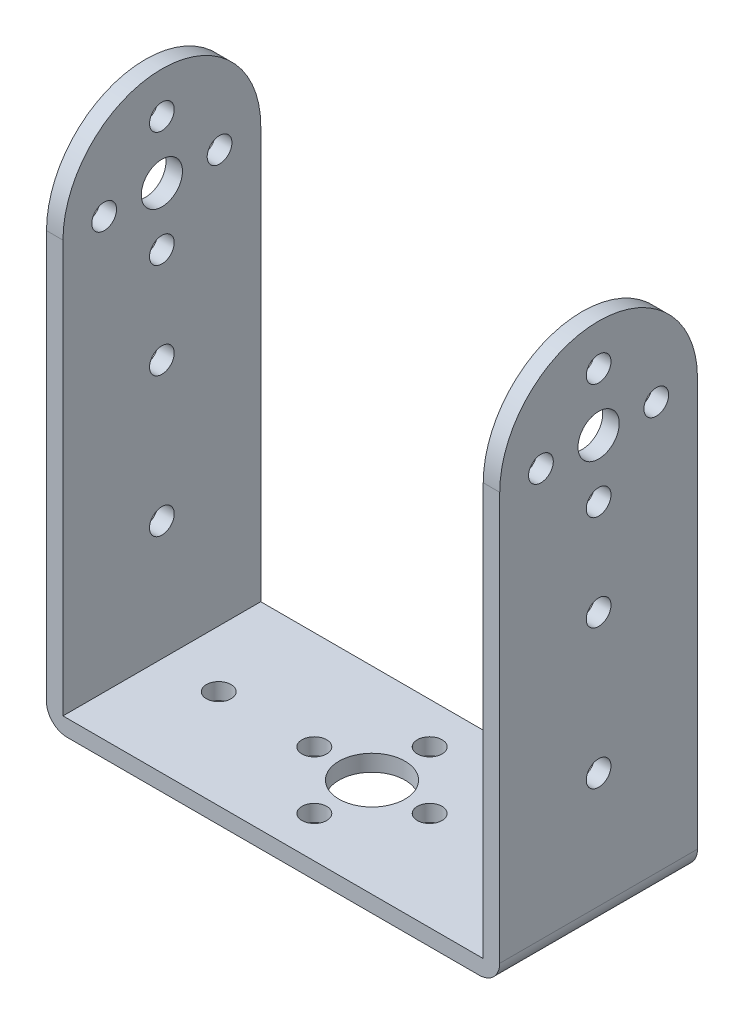
SolidWorks part; units mm, degrees
ref_plane "Front Plane" through (0, 0, 0) normal (0, 0, 1) x (1, 0, 0)
ref_plane "Top Plane" through (0, 0, 0) normal (0, 1, 0) x (1, 0, 0)
ref_plane "Right Plane" through (0, 0, 0) normal (1, 0, 0) x (0, 0, -1)
sketch "Sketch2" plane through (0, 0, 0) normal (0, 1, 0) x (1, 0, 0)
  line L0 (0, 1.0872) -> (0, 23.0088) construction
  line L1 (-27.5, -12) -> (27.5, -12)
  line L2 (-27.5, -12) -> (-27.5, 12)
  line L3 (-27.5, 12) -> (27.5, 12)
  line L4 (27.5, -12) -> (27.5, 12)
  line L5 (-27.5, -12) -> (27.5, 12) construction
  line L6 (-27.5, 12) -> (27.5, -12) construction
  line L7 (0, 0) -> (61.8612, 0) construction
  circle A0 centre (0, 0) radius 4
  circle A1 centre (0, 0) radius 7 construction
  circle A2 centre (0, 7) radius 1.5
  circle A3 centre (7, 0) radius 1.5
  circle A4 centre (0, -7) radius 1.5
  circle A5 centre (-7, 0) radius 1.5
  circle A6 centre (-18.6, 0) radius 1.5
  circle A7 centre (18.6, 0) radius 1.5
  point P0 (0, 0)
  point P24 (0, 0)
  dimension "D3" = 8
  dimension "D4" = 14
  dimension "D5" = 3
  dimension "D7" = 3
  dimension "D8" = 37.2
  dimension "D1" = 55
  dimension "D2" = 24
  dimension "D6" = 4
extrude "Boss-Extrude1" add sketch "Sketch2" along normal blind 2
sketch "Sketch5" plane through (-27.5, 0, 0) normal (-1, 0, 0) x (0, 0, 1)
  line L0 (12, 0) -> (12, 52)
  line L1 (-12, 52) -> (-12, 0)
  line L3 (12, 0) -> (-12, 0)
  line L4 (0, 68.1399) -> (0, 42.3246) construction
  line L5 (10.8254, 52) -> (-17.3303, 52) construction
  arc A1 (12, 52) -> (-12, 52) centre (0, 52) ccw
  circle A2 centre (0, 52) radius 2.5
  circle A3 centre (0, 52) radius 7 construction
  circle A4 centre (0, 59) radius 1.5
  circle A5 centre (7, 52) radius 1.5
  circle A6 centre (0, 45) radius 1.5
  circle A7 centre (-7, 52) radius 1.5
  circle A8 centre (0, 33.4) radius 1.5
  circle A9 centre (0, 16.5) radius 1.5
  point P25 (0, 52)
  point P29 (0, 64)
  dimension "D1" = 52
  dimension "D2" = 5
  dimension "D3" = 14
  dimension "D4" = 3
  dimension "D6" = 3
  dimension "D7" = 3
  dimension "D8" = 16.9
  dimension "D9" = 16.5
  dimension "D10" = 30.6
  dimension "D5" = 4
extrude "Boss-Extrude2" add sketch "Sketch5" against normal blind 2
mirror "Mirror1" about plane through (0, 0, 0) normal (1, 0, 0) of "Boss-Extrude2"
fillet "Fillet1" radius 2.5 2 edges at (27.5, 0, 0) (-27.5, 0, 0)
